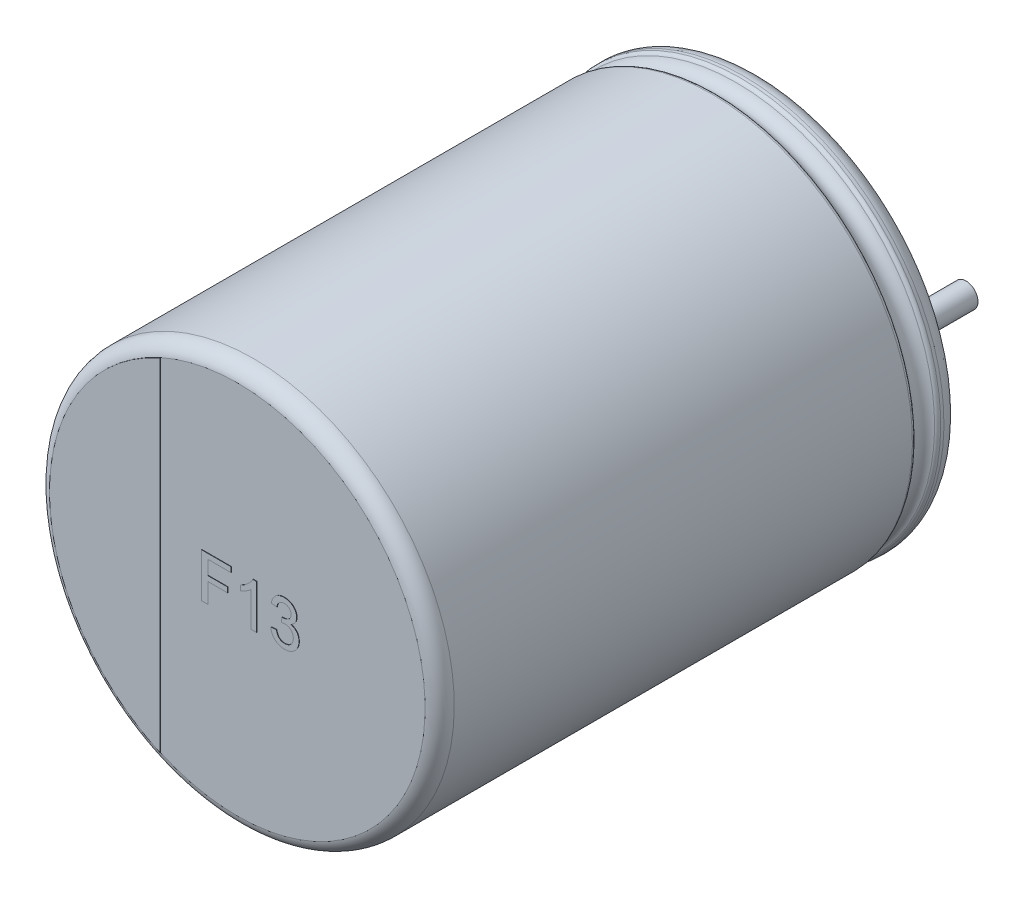
SolidWorks part; units mm, degrees
ref_plane "Plan de face" through (0, 0, 0) normal (0, 0, 1) x (1, 0, 0)
ref_plane "Plan de dessus" through (0, 0, 0) normal (0, 1, 0) x (1, 0, 0)
ref_plane "Plan de droite" through (0, 0, 0) normal (1, 0, 0) x (0, 0, -1)
sketch "Sketch10" plane through (0, 0, 0) normal (1, 0, 0) x (0, 0, -1)
  line L0 (18.1631, 0) -> (-18.9631, 0) construction
  line L1 (-13, 0) -> (-0.05, 0)
  line L2 (-13, 0) -> (-13, 4.6736)
  line L3 (-12.6, 5) -> (-1.1846, 5)
  line L4 (-0.05, 4.4031) -> (-0.05, 0)
  line L7 (-0.4794, 5) -> (-0.3982, 5)
  arc A0 (-13, 4.6736) -> (-12.6, 5) centre (-12.6068, 4.6001) cw
  arc A1 (-0.3982, 5) -> (-0.05, 4.4031) centre (-0.3982, 4.6) cw
  arc A2 (-0.5713, 4.9394) -> (-1.0926, 4.9394) centre (-0.832, 5.051) cw
  arc A3 (-1.0926, 4.9394) -> (-1.1846, 5) centre (-1.1846, 4.9) ccw
  arc A4 (-0.5713, 4.9394) -> (-0.4794, 5) centre (-0.4794, 4.9) cw
  point P4 (0.57, 0)
  point P13 (-13, 5)
  dimension "D2" = 0.4
  dimension "D3" = 0.4
  dimension "D4" = 0.1
  dimension "D5" = 0.1
  dimension "D1" = 5
revolve "Повернуть1" add sketch "Sketch10" angle 360 about L0
sketch "Эскиз2" plane through (0, 0, 0.05) normal (0, 0, -1) x (-1, 0, 0)
  line L1 (0, 0.7993) -> (0, -1.0496) construction
  line L2 (-2.5, 0) -> (2.3813, 0) construction
  circle A3 centre (-2.5, 0) radius 0.3
  circle A7 centre (2.5, 0) radius 0.3
  dimension "D1" = 5
extrude "Бобышка-Вытянуть1" add sketch "Эскиз2" along normal blind 2.7
sketch "Эскиз4" plane through (0, 0, 13) normal (0, 0, 1) x (1, 0, 0)
  line L0 (-1.9206, -4.2607) -> (-1.9206, 4.2607)
  circle A1 centre (0, 0) radius 4.6736 construction
  arc A2 (-1.9206, 4.2607) -> (-1.9206, -4.2607) centre (0, 0) ccw
extrude "Бобышка-Вытянуть2" add sketch "Эскиз4" along normal blind 0.01
sketch "Эскиз5" plane through (0, 0, 13) normal (0, 0, 1) x (1, 0, 0)
  text T0 "F13" font "Arial" height 1.1
extrude "Текст" add sketch "Эскиз5" along normal blind 0.01
sketch "Эскиз6" plane through (0, 0, 0.05) normal (0, 0, -1) x (-1, 0, 0)
  line L0 (-2.5, 0.6247) -> (-2.6072, 0.6247)
  line L1 (-2.5, -0.6247) -> (-2.6072, -0.6247)
  line L2 (2.5, -0.6247) -> (2.6072, -0.6247)
  line L3 (2.5, 0.6247) -> (2.6072, 0.6247)
  arc A0 (-2.8442, -0.9542) -> (2.8442, -0.9542) centre (0, 0) ccw
  arc A1 (-2.5, -0.6247) -> (-2.5, 0.6247) centre (-2.5, 0) ccw
  arc A2 (2.5, 0.6247) -> (2.5, -0.6247) centre (2.5, 0) ccw
  arc A3 (2.8442, 0.9542) -> (-2.8442, 0.9542) centre (0, 0) ccw
  arc A4 (2.6072, 0.6247) -> (2.8442, 0.9542) centre (2.6072, 0.8747) ccw
  arc A5 (2.6072, -0.6247) -> (2.8442, -0.9542) centre (2.6072, -0.8747) cw
  arc A6 (-2.8442, -0.9542) -> (-2.6072, -0.6247) centre (-2.6072, -0.8747) cw
  arc A7 (-2.6072, 0.6247) -> (-2.8442, 0.9542) centre (-2.6072, 0.8747) cw
  point P7 (2.9342, 0.6247)
  point P23 (0, -3)
  point P24 (0, 3)
  dimension "D1" = 0.25
  dimension "D2" = 6
extrude "Бобышка-Вытянуть5" add sketch "Эскиз6" along normal blind 0.05 contours A3 A7 L0 A1 L1 A6 A0 A5 L2 A2 L3 A4
